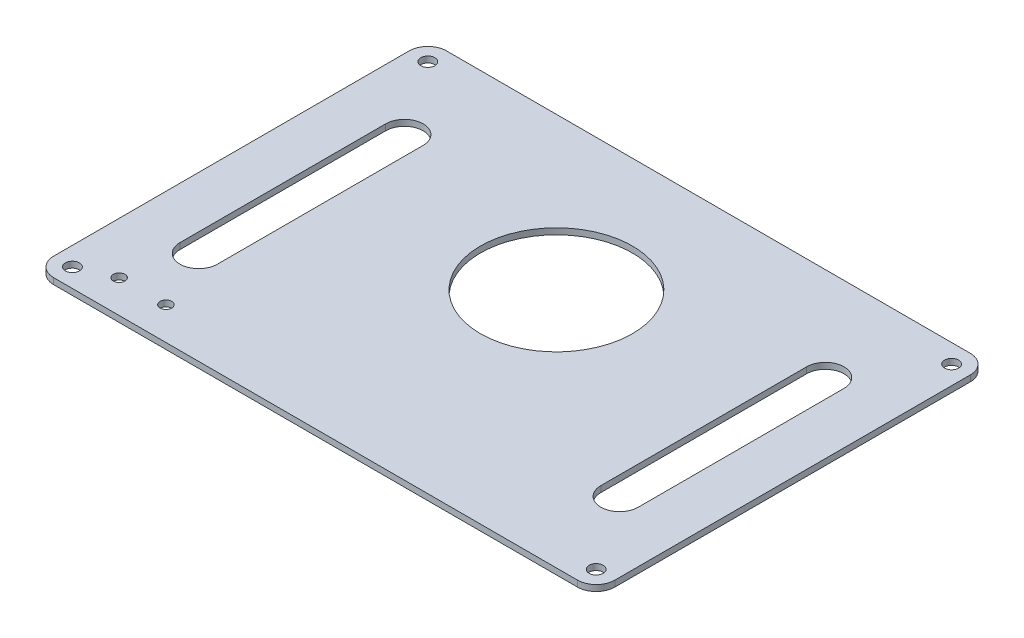
SolidWorks part; units mm, degrees
ref_plane "Front Plane" through (0, 0, 0) normal (0, 0, 1) x (1, 0, 0)
ref_plane "Top Plane" through (0, 0, 0) normal (0, 1, 0) x (1, 0, 0)
ref_plane "Right Plane" through (0, 0, 0) normal (1, 0, 0) x (0, 0, -1)
sketch "Sketch1" plane through (0, 0, 0) normal (0, 1, 0) x (1, 0, 0)
  line L1 (-56, -42) -> (56, -42)
  line L2 (-60, -38) -> (-60, 38)
  line L3 (-56, 42) -> (56, 42)
  line L4 (60, -38) -> (60, 38)
  line L5 (-58.6127, -41.0289) -> (58.6127, 41.0289) construction
  line L6 (-58.6127, 41.0289) -> (58.6127, -41.0289) construction
  arc A0 (-56, 42) -> (-60, 38) centre (-56, 38) ccw
  arc A1 (60, 38) -> (56, 42) centre (56, 38) ccw
  arc A2 (56, -42) -> (60, -38) centre (56, -38) ccw
  arc A3 (-60, -38) -> (-56, -42) centre (-56, -38) ccw
  circle A4 centre (-56, 38) radius 1.5
  circle A5 centre (56, 38) radius 1.5
  circle A6 centre (56, -38) radius 1.5
  circle A7 centre (-56, -38) radius 1.5
  point P0 (0, 0)
  dimension "D3" = 8
  dimension "D1" = 3
  dimension "D2" = 3
  dimension "D6" = 3
  dimension "D7" = 3
  dimension "D4" = 2
  dimension "D5" = 2
extrude "Boss-Extrude1" add sketch "Sketch1" along normal blind 1.3
sketch "Sketch2" plane through (0, 1.3, 0) normal (0, 1, 0) x (1, 0, 0)
  line L0 (56, 42) -> (-56, 42) construction
  line L1 (-60, 38) -> (-60, -38) construction
  line L2 (-56, -42) -> (56, -42) construction
  line L3 (0, 25.75) -> (0, -42) construction
  line L5 (-49, 22) -> (-49, -22)
  line L7 (-41, 22) -> (-41, -22)
  line L8 (49, 22) -> (49, -22)
  line L9 (41, 22) -> (41, -22)
  circle A0 centre (0, 9.5) radius 16.25
  arc A1 (-41, 22) -> (-49, 22) centre (-45, 22) ccw
  arc A2 (-49, -22) -> (-41, -22) centre (-45, -22) ccw
  arc A3 (41, 22) -> (49, 22) centre (45, 22) cw
  arc A4 (49, -22) -> (41, -22) centre (45, -22) cw
  circle A5 centre (-49, -35) radius 1.25
  circle A6 centre (-39, -35) radius 1.25
  dimension "D1" = 32.5
  dimension "D2" = 32.5
  dimension "D3" = 8
  dimension "D4" = 20
  dimension "D5" = 15
  dimension "D6" = 8
  dimension "D7" = 20
  dimension "D8" = 15
  dimension "D9" = 11
  dimension "D10" = 7
  dimension "D11" = 2.5
  dimension "D12" = 2.5
  dimension "D13" = 10
extrude "Cut-Extrude1" cut sketch "Sketch2" against normal blind 1.3
